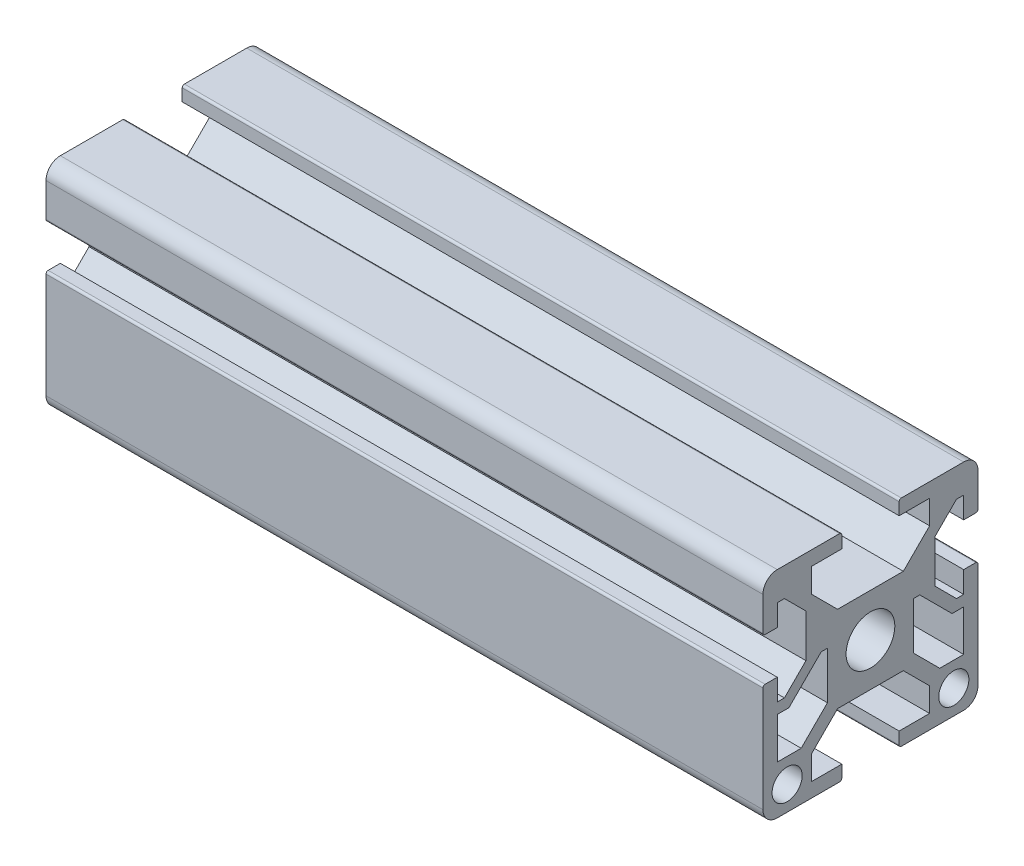
SolidWorks part; units mm, degrees
material "A6N01SS-T5"
ref_plane "Front Plane" through (0, 0, 0) normal (0, 0, 1) x (1, 0, 0)
ref_plane "Top Plane" through (0, 0, 0) normal (0, 1, 0) x (1, 0, 0)
ref_plane "Right Plane" through (0, 0, 0) normal (1, 0, 0) x (0, 0, -1)
sketch "Sketch1" plane through (0, 0, 0) normal (1, 0, 0) x (0, 0, -1)
  line L0 (-13, -2.5) -> (-13, -8.25)
  line L1 (-11.3787, -2.5) -> (-13, -2.5)
  line L2 (-6.8787, 2) -> (-11.3787, -2.5)
  line L3 (-6, 2) -> (-6.8787, 2)
  line L4 (-6, -4.5858) -> (-6, 2)
  line L5 (-9.6642, -8.25) -> (-6, -4.5858)
  line L6 (-13, -8.25) -> (-9.6642, -8.25)
  line L7 (6, 2) -> (6, -4.5858)
  line L8 (6.8787, 2) -> (6, 2)
  line L9 (11.3787, -2.5) -> (6.8787, 2)
  line L10 (13, -2.5) -> (11.3787, -2.5)
  line L11 (13, -8.25) -> (13, -2.5)
  line L12 (9.6642, -8.25) -> (13, -8.25)
  line L13 (6, -4.5858) -> (9.6642, -8.25)
  line L14 (-15, 1.7) -> (-15, -13)
  line L15 (-13, -15) -> (-4.3, -15)
  line L16 (-4, -14.7) -> (-4, -13)
  line L17 (-4, -13) -> (-8.25, -13)
  line L18 (-8.25, -13) -> (-8.25, -9.6642)
  line L19 (-8.25, -9.6642) -> (-4.5858, -6)
  line L20 (-4.5858, -6) -> (4.5858, -6)
  line L24 (4.5858, -6) -> (8.25, -9.6642)
  line L25 (8.25, -9.6642) -> (8.25, -13)
  line L26 (8.25, -13) -> (4, -13)
  line L27 (4, -13) -> (4, -14.7)
  line L28 (4.3, -15) -> (13, -15)
  line L29 (15, -13) -> (15, 1.7)
  line L30 (14.7, 2) -> (13, 2)
  line L31 (13, 2) -> (13, -1)
  line L32 (13, -1) -> (12, -1)
  line L33 (12, -1) -> (9, 2)
  line L34 (9, 2) -> (9, 8)
  line L38 (9, 8) -> (12, 11)
  line L39 (12, 11) -> (13, 11)
  line L40 (13, 11) -> (13, 8)
  line L41 (13, 8) -> (14.7, 8)
  line L42 (15, 8.3) -> (15, 13)
  line L43 (13, 15) -> (4.3, 15)
  line L44 (4, 14.7) -> (4, 13)
  line L45 (4, 13) -> (8.25, 13)
  line L46 (8.25, 13) -> (8.25, 9.6642)
  line L47 (8.25, 9.6642) -> (4.5858, 6)
  line L51 (4.5858, 6) -> (-4.5858, 6)
  line L52 (-4.5858, 6) -> (-8.25, 9.6642)
  line L53 (-8.25, 9.6642) -> (-8.25, 13)
  line L54 (-8.25, 13) -> (-4, 13)
  line L55 (-4, 13) -> (-4, 14.7)
  line L56 (-4.3, 15) -> (-13, 15)
  line L57 (-15, 13) -> (-15, 8.3)
  line L58 (-14.7, 8) -> (-13, 8)
  line L59 (-13, 8) -> (-13, 11)
  line L60 (-13, 11) -> (-12, 11)
  line L61 (-12, 11) -> (-9, 8)
  line L65 (-9, 8) -> (-9, 2)
  line L66 (-9, 2) -> (-12, -1)
  line L67 (-12, -1) -> (-13, -1)
  line L68 (-13, -1) -> (-13, 2)
  line L69 (-13, 2) -> (-14.7, 2)
  circle A0 centre (0, 0) radius 3.4
  circle A1 centre (-11.625, -11.625) radius 2.1
  circle A2 centre (11.625, -11.625) radius 2.1
  arc A3 (-15, -13) -> (-13, -15) centre (-13, -13) ccw
  arc A4 (-4.3, -15) -> (-4, -14.7) centre (-4.3, -14.7) ccw
  arc A5 (4, -14.7) -> (4.3, -15) centre (4.3, -14.7) ccw
  arc A6 (13, -15) -> (15, -13) centre (13, -13) ccw
  arc A7 (15, 1.7) -> (14.7, 2) centre (14.7, 1.7) ccw
  arc A8 (14.7, 8) -> (15, 8.3) centre (14.7, 8.3) ccw
  arc A9 (15, 13) -> (13, 15) centre (13, 13) ccw
  arc A10 (4.3, 15) -> (4, 14.7) centre (4.3, 14.7) ccw
  arc A11 (-4, 14.7) -> (-4.3, 15) centre (-4.3, 14.7) ccw
  arc A12 (-13, 15) -> (-15, 13) centre (-13, 13) ccw
  arc A13 (-15, 8.3) -> (-14.7, 8) centre (-14.7, 8.3) ccw
  arc A14 (-14.7, 2) -> (-15, 1.7) centre (-14.7, 1.7) ccw
  dimension "A" = 30
  dimension "B" = 30
extrude "Boss-Extrude1" add sketch "Sketch1" along normal blind 100
ref_plane "Plane1" through (0, 0, 0) normal (1, 0, 0) x (0, 0, -1)
ref_plane "Plane2" through (100, 0, 0) normal (1, 0, 0) x (0, 0, -1)
sketch "Sketch2" [suppressed] plane through (0, 0, 0) normal (1, 0, 0) x (0, 0, -1)
  circle A0 centre (0, 0) radius 3.4
  dimension "FIX_2" = 6.8
extrude "Boss-Extrude2" [suppressed] add sketch "Sketch2" along normal blind 24
hole_wizard "Tapped Hole1" [suppressed] positions "Sketch4" profile "Sketch3" tap size "M8x1.25" standard "JIS"
sketch "Sketch4" [suppressed] plane through (0, 0, 22.6056) normal (1, 0, 0) x (0, 0, -1)
  point P0 (22.6056, 0)
sketch "Sketch3" [suppressed] plane through (0, 0, 0) normal (0, 1, 0) x (0, 0, 1)
  line L0 (0, 0) -> (0, 24)
  line L1 (0, 24) -> (3.4, 24)
  line L2 (3.4, 24) -> (3.4, 0)
  line L5 (3.4, 0) -> (0, 0)
  line L11 (0, -6.35) -> (0, 107.95) construction
  dimension "Thru Tap Drill Dia." = 6.8
  dimension "Thru Tap Drill Depth" = 24
cosmetic thread "Hole Thread1" [suppressed] parameters "NFIX_2"=24, "NFIX_1"=8
sketch "Sketch5" [suppressed] plane through (50, 0, 0) normal (1, 0, 0) x (0, 0, -1)
  circle A0 centre (0, 0) radius 3.4
  dimension "FIX_4" = 6.8
extrude "Boss-Extrude3" [suppressed] add sketch "Sketch5" against normal blind 24
hole_wizard "Tapped Hole2" [suppressed] positions "Sketch7" profile "Sketch6" tap size "M8x1.25" standard "JIS"
sketch "Sketch7" [suppressed] plane through (50, 0, -42.1055) normal (-1, 0, 0) x (0, 0, 1)
  point P0 (42.1055, 0)
sketch "Sketch6" [suppressed] plane through (50, 0, 0) normal (0, 1, 0) x (0, 0, -1)
  line L0 (0, 0) -> (0, 24)
  line L1 (0, 24) -> (3.4, 24)
  line L2 (3.4, 24) -> (3.4, 0)
  line L5 (3.4, 0) -> (0, 0)
  line L11 (0, -6.35) -> (0, 107.95) construction
  dimension "Thru Tap Drill Dia." = 6.8
  dimension "Thru Tap Drill Depth" = 24
cosmetic thread "Hole Thread2" [suppressed] parameters "NFIX_2"=24, "NFIX_1"=8
sketch "Sketch8" [suppressed] plane through (0, 0, 0) normal (1, 0, 0) x (0, 0, -1)
  circle A0 centre (0, 0) radius 3.4
  dimension "FIX_6" = 6.8
extrude "Boss-Extrude4" [suppressed] add sketch "Sketch8" along normal blind 24
sketch "Sketch9" [suppressed] plane through (50, 0, 0) normal (1, 0, 0) x (0, 0, -1)
  circle A0 centre (0, 0) radius 3.4
  dimension "FIX_8" = 6.8
extrude "Boss-Extrude5" [suppressed] add sketch "Sketch9" against normal blind 24
hole_wizard "Tapped Hole3" [suppressed] positions "Sketch11" profile "Sketch10" tap size "M8x1.25" standard "JIS"
sketch "Sketch11" [suppressed] plane through (0, 0, 65.6224) normal (1, 0, 0) x (0, 0, -1)
  point P0 (65.6224, 0)
sketch "Sketch10" [suppressed] plane through (0, 0, 0) normal (0, 1, 0) x (0, 0, 1)
  line L0 (0, 0) -> (0, 24)
  line L1 (0, 24) -> (3.4, 24)
  line L2 (3.4, 24) -> (3.4, 0)
  line L5 (3.4, 0) -> (0, 0)
  line L11 (0, -6.35) -> (0, 107.95) construction
  dimension "Thru Tap Drill Dia." = 6.8
  dimension "Thru Tap Drill Depth" = 24
cosmetic thread "Hole Thread3" [suppressed] parameters "NFIX_2"=24, "NFIX_1"=8
hole_wizard "Tapped Hole4" [suppressed] positions "Sketch13" profile "Sketch12" tap size "M8x1.25" standard "JIS"
sketch "Sketch13" [suppressed] plane through (50, 0, -73.8986) normal (-1, 0, 0) x (0, 0, 1)
  point P0 (73.8986, 0)
sketch "Sketch12" [suppressed] plane through (50, 0, 0) normal (0, 1, 0) x (0, 0, -1)
  line L0 (0, 0) -> (0, 24)
  line L1 (0, 24) -> (3.4, 24)
  line L2 (3.4, 24) -> (3.4, 0)
  line L5 (3.4, 0) -> (0, 0)
  line L11 (0, -6.35) -> (0, 107.95) construction
  dimension "Thru Tap Drill Dia." = 6.8
  dimension "Thru Tap Drill Depth" = 24
cosmetic thread "Hole Thread4" [suppressed] parameters "NFIX_2"=24, "NFIX_1"=8
chamfer "Chamfer1" [suppressed] distance 0.2 angle 45
